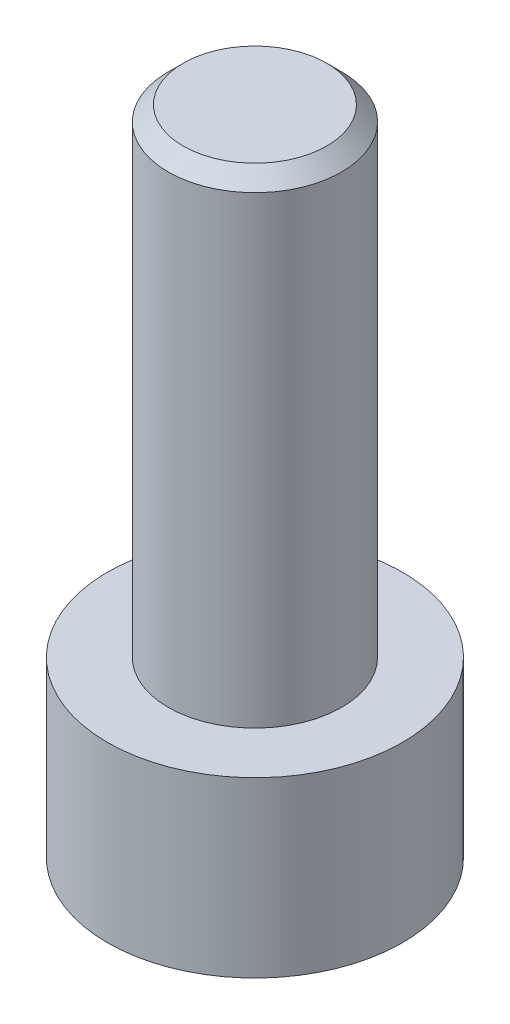
SolidWorks part; units mm, degrees
material "201 Annealed Stainless Steel (SS)"
ref_plane "Front Plane" through (0, 0, 0) normal (0, 0, 1) x (1, 0, 0)
ref_plane "Top Plane" through (0, 0, 0) normal (0, 1, 0) x (1, 0, 0)
ref_plane "Right Plane" through (0, 0, 0) normal (1, 0, 0) x (0, 0, -1)
sketch "Sketch1" plane through (0, 0, 0) normal (0, 1, 0) x (1, 0, 0)
  circle A0 centre (0, 0) radius 2.465
  dimension "D1" = 4.93
extrude "Boss-Extrude1" add sketch "Sketch1" along normal blind 2.9
sketch "Sketch2" plane through (0, 2.9, 0) normal (0, 1, 0) x (1, 0, 0)
  circle A0 centre (0, 0) radius 1.45
  dimension "D1" = 2.9
extrude "Boss-Extrude2" add sketch "Sketch2" along normal blind 8
sketch "Sketch3" plane through (0, 0, 0) normal (0, -1, 0) x (1, 0, 0)
  line L1 (0.7332, -1.27) -> (1.4665, 0)
  line L2 (1.4665, 0) -> (0.7332, 1.27)
  line L3 (0.7332, 1.27) -> (-0.7332, 1.27)
  line L4 (-0.7332, 1.27) -> (-1.4665, 0)
  line L5 (-1.4665, 0) -> (-0.7332, -1.27)
  line L6 (-0.7332, -1.27) -> (0.7332, -1.27)
  circle A0 centre (0, 0) radius 1.27 construction
  dimension "D1" = 2.54
extrude "Cut-Extrude1" cut sketch "Sketch3" against normal blind 1.9
chamfer "Chamfer1" distance 0.25 angle 45 1 edges at (0, 10.9, 1.45)
